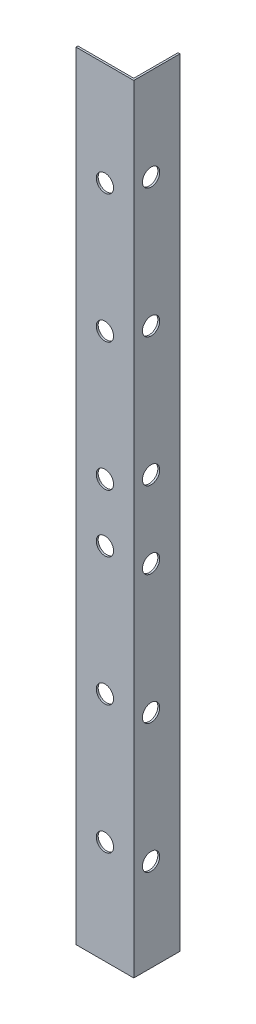
SolidWorks part; units mm, degrees
material "6061-T6 (SS)"
ref_plane "Alzado" through (0, 0, 0) normal (0, 0, 1) x (1, 0, 0)
ref_plane "Planta" through (0, 0, 0) normal (0, 1, 0) x (1, 0, 0)
ref_plane "Vista lateral" through (0, 0, 0) normal (1, 0, 0) x (0, 0, -1)
sketch "Sketch1" plane through (0, 0, 0) normal (0, 1, 0) x (1, 0, 0)
  line L0 (0, 0) -> (15, 0)
  line L1 (15, 0) -> (15, 12)
  line L2 (15, 12) -> (14.5, 12)
  line L3 (14.5, 12) -> (14.5, 0.5)
  line L4 (14.5, 0.5) -> (0, 0.5)
  line L5 (0, 0.5) -> (0, 0)
  dimension "D1" = 15
  dimension "D2" = 12
  dimension "D3" = 0.5
  dimension "D4" = 0.5
extrude "Boss-Extrude1" add sketch "Sketch1" along normal blind 202
sketch "Sketch2" plane through (0, 0, 0) normal (0, 0, 1) x (1, 0, 0)
  circle A0 centre (7.5, 175.1667) radius 2.25
  circle A1 centre (7.5, 141.8333) radius 2.25
  circle A2 centre (7.5, 108.5) radius 2.25
  circle A3 centre (7.5, 93.5) radius 2.25
  circle A4 centre (7.5, 60.1667) radius 2.25
  circle A5 centre (7.5, 26.8333) radius 2.25
  dimension "D1" = 4.5
extrude "Cut-Extrude1" cut sketch "Sketch2" against normal up to next
sketch "Sketch3" plane through (15, 0, 0) normal (1, 0, 0) x (0, 0, -1)
  circle A0 centre (4.5, 24) radius 2.25
  circle A1 centre (4.5, 57.5) radius 2.25
  circle A2 centre (4.5, 91) radius 2.25
  circle A3 centre (4.5, 111) radius 2.25
  circle A4 centre (4.5, 144.5) radius 2.25
  circle A5 centre (4.5, 178) radius 2.25
  dimension "D1" = 4.5
extrude "Cut-Extrude2" cut sketch "Sketch3" against normal up to next
